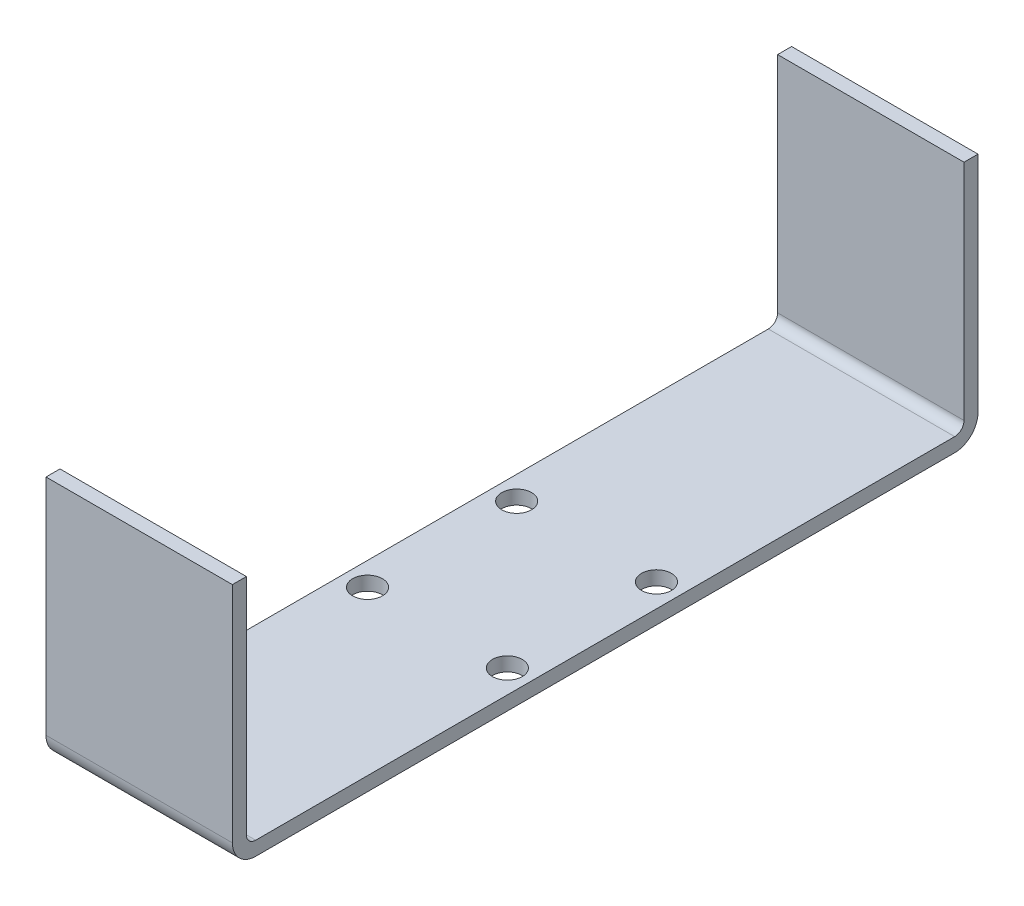
SolidWorks part; units mm, degrees
ref_plane "Front Plane" through (0, 0, 0) normal (0, 0, 1) x (1, 0, 0)
ref_plane "Top Plane" through (0, 0, 0) normal (0, 1, 0) x (1, 0, 0)
ref_plane "Right Plane" through (0, 0, 0) normal (1, 0, 0) x (0, 0, -1)
sketch "Sketch2" plane through (0, 0, 0) normal (0, 1, 0) x (1, 0, 0)
  line L0 (-7.5, 8) -> (7.5, 8) construction
  line L1 (-10, 40) -> (10, 40)
  line L2 (-10, 40) -> (-10, -40)
  line L3 (-10, -40) -> (10, -40)
  line L4 (10, 40) -> (10, -40)
  line L5 (-10, 40) -> (10, -40) construction
  line L6 (-10, -40) -> (10, 40) construction
  line L7 (7.5, 8) -> (7.5, -8) construction
  line L8 (7.5, -8) -> (-7.5, -8) construction
  line L9 (-7.5, -8) -> (-7.5, 8) construction
  line L10 (0, 8) -> (0, -8) construction
  line L11 (10, 0) -> (-10, 0) construction
  circle A0 centre (-7.5, 8) radius 1.6
  circle A1 centre (7.5, 8) radius 1.6
  circle A2 centre (-7.5, -8) radius 1.6
  circle A3 centre (7.5, -8) radius 1.6
  point P0 (0, 0)
  point P18 (0, 0)
  point P19 (12.8071, 0)
  point P20 (0, 8)
  point P21 (-40, 2.9722)
  point P22 (0, 0)
  point P23 (14.4077, 0)
  dimension "D3" = 3.2
  dimension "D1" = 80
  dimension "D2" = 20
  dimension "D4" = 15
  dimension "D5" = 16
extrude "Boss-Extrude1" add sketch "Sketch2" along normal blind 1.5
sketch "Sketch3" plane through (0, 1.5, 0) normal (0, 1, 0) x (1, 0, 0)
  line L0 (10, -40) -> (10, 40) construction
  line L1 (-10, 40) -> (10, 40)
  line L2 (-10, 40) -> (-10, 38.5)
  line L3 (-10, 38.5) -> (10, 38.5)
  line L4 (10, 40) -> (10, 38.5)
  line L6 (-10, -40) -> (10, -40)
  line L7 (-10, -40) -> (-10, -38.5)
  line L8 (-10, -38.5) -> (10, -38.5)
  line L9 (10, -40) -> (10, -38.5)
  point P11 (0, 0)
  point P12 (10, -46.4529)
  dimension "D1" = 1.5
  dimension "D2" = 1.5
extrude "Boss-Extrude2" add sketch "Sketch3" along normal blind 25
fillet "Fillet1" radius 1 2 edges at (0, 1.5, 38.5) (0, 1.5, -38.5)
fillet "Fillet2" radius 2.5 2 edges at (0, 0, 40) (0, 0, -40)
